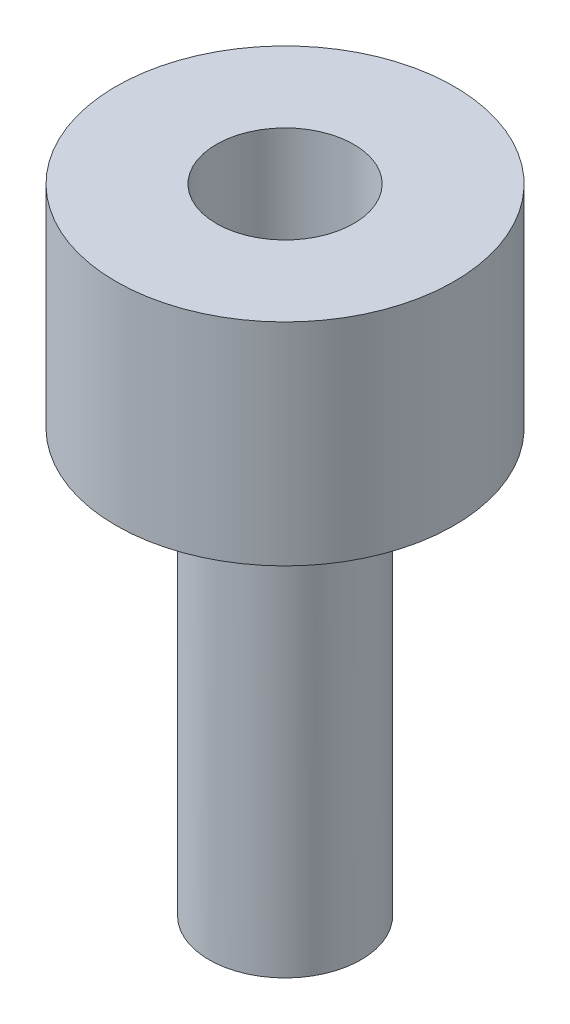
SolidWorks part; units mm, degrees
ref_plane "Front Plane" through (0, 0, 0) normal (0, 0, 1) x (1, 0, 0)
ref_plane "Top Plane" through (0, 0, 0) normal (0, 1, 0) x (1, 0, 0)
ref_plane "Right Plane" through (0, 0, 0) normal (1, 0, 0) x (0, 0, -1)
sketch "Sketch1" plane through (0, 0, 0) normal (0, 1, 0) x (1, 0, 0)
  circle A0 centre (0, 0) radius 3.6
  dimension "D1" = 7.2
extrude "Boss-Extrude1" add sketch "Sketch1" along normal blind 10
sketch "Sketch2" plane through (0, 10, 0) normal (0, 1, 0) x (1, 0, 0)
  circle A0 centre (0, 0) radius 8
extrude "Boss-Extrude2" add sketch "Sketch2" along normal blind 10
sketch "Sketch3" plane through (0, 20, 0) normal (0, 1, 0) x (1, 0, 0)
  circle A0 centre (0, 0) radius 3.25
  circle A1 centre (0, 0) radius 8 construction
  dimension "D1" = 6.5
extrude "Cut-Extrude1" cut sketch "Sketch3" against normal blind 8
sketch "Sketch4" plane through (0, 0, 0) normal (0, -1, 0) x (1, 0, 0)
  circle A1 centre (0, 0) radius 3.6
  circle A2 centre (0, 0) radius 3.6
  dimension "D1" = 0
extrude "Boss-Extrude3" add sketch "Sketch4" along normal blind 10
fillet "Fillet1" radius 2 1 edges at (0, 10, 3.6)
